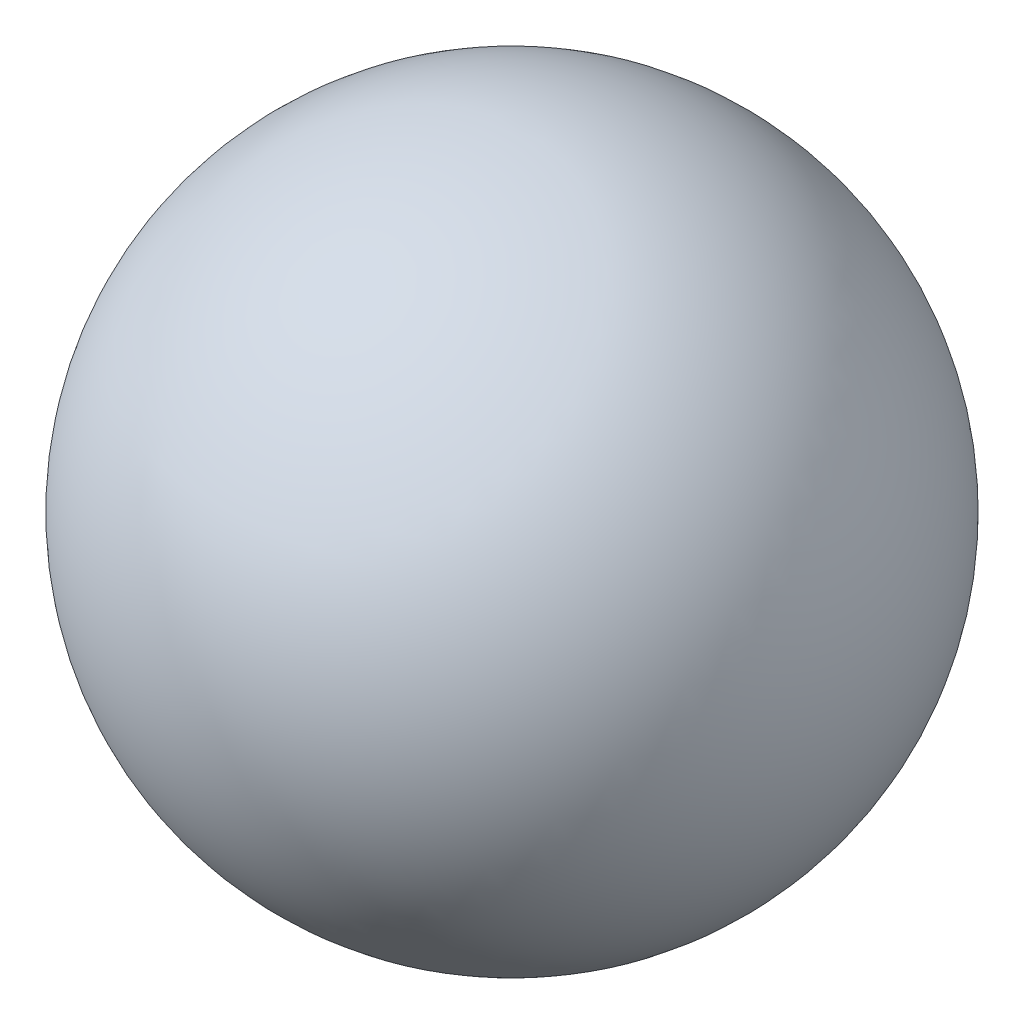
SolidWorks part; units mm, degrees
ref_plane "Front Plane" through (0, 0, 0) normal (0, 0, 1) x (1, 0, 0)
ref_plane "Top Plane" through (0, 0, 0) normal (0, 1, 0) x (1, 0, 0)
ref_plane "Right Plane" through (0, 0, 0) normal (1, 0, 0) x (0, 0, -1)
sketch "Sketch1" plane through (0, 0, 0) normal (0, 0, 1) x (1, 0, 0)
  line L0 (0, -9.525) -> (0, 9.525)
  arc A0 (0, -9.525) -> (0, 9.525) centre (0, 0) ccw
  dimension "D1" = 19.05
revolve "Revolve4" add sketch "Sketch1" angle 360 about L0
